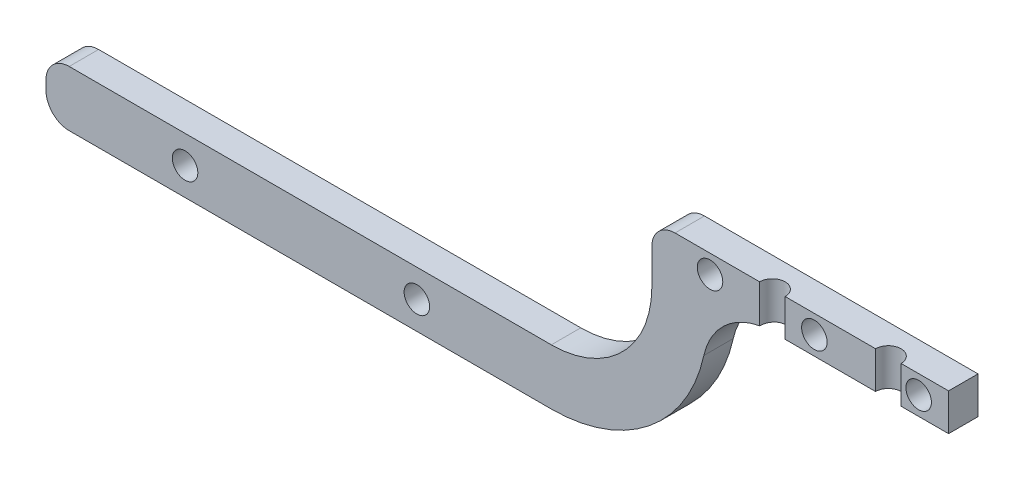
SolidWorks part; units mm, degrees
ref_plane "Front Plane" through (0, 0, 0) normal (0, 0, 1) x (1, 0, 0)
ref_plane "Top Plane" through (0, 0, 0) normal (0, 1, 0) x (1, 0, 0)
ref_plane "Right Plane" through (0, 0, 0) normal (1, 0, 0) x (0, 0, -1)
sketch "Sketch1" plane through (0, 0, 0) normal (0, 0, 1) x (1, 0, 0)
  line L0 (0, 0) -> (-64, 0)
  line L1 (-64, 0) -> (-64, -12.5522)
  line L2 (0, 0) -> (0, -8)
  line L3 (0, -8) -> (-52, -8)
  line L4 (-85.6878, -34.24) -> (-194.6878, -34.24)
  line L5 (-194.6878, -34.24) -> (-194.6878, -46.24)
  line L6 (-194.6878, -46.24) -> (-85.6878, -46.24)
  line L7 (-52, -12.5522) -> (-52, -8)
  arc A0 (-64, -12.5522) -> (-85.6878, -34.24) centre (-85.6878, -12.5522) cw
  arc A2 (-85.6878, -46.24) -> (-52, -12.5522) centre (-85.6878, -12.5522) ccw
  dimension "D4" = 4.5522
  dimension "D1" = 64
  dimension "D2" = 8
  dimension "D3" = 26.24
  dimension "D5" = 109
  dimension "D6" = 12
extrude "Boss-Extrude1" add sketch "Sketch1" along normal blind 6.35
fillet "Fillet1" radius 5 3 edges at (-64, 0, 3.175) (-194.6878, -46.24, 3.175) (-194.6878, -34.24, 3.175)
sketch "Sketch3" plane through (0, 0, 0) normal (0, 1, 0) x (1, 0, 0)
  line L0 (0, -3.175) -> (-59, -3.175) construction
  line L1 (0, -6.35) -> (0, 0) construction
  line L2 (-59, 0) -> (-59, -6.35) construction
  line L4 (0, -6.35) -> (-59, -6.35) construction
  circle A0 centre (-13, -6.35) radius 2.75
  circle A1 centre (-38, -6.35) radius 2.75
  point P8 (0, 0)
  point P11 (0, 0)
  point P12 (0, 0)
  point P13 (0, 0)
  point P14 (-38, -6.35)
  dimension "D1" = 5.5
  dimension "D2" = 5.5
  dimension "D3" = 25
  dimension "D4" = 13
fillet "Fillet2" radius 15 1 edges at (-52, -8, 3.175)
sketch "Sketch4" plane through (0, 0, 6.35) normal (0, 0, 1) x (1, 0, 0)
  line L0 (-181.7526, -34.24) -> (-181.7526, -46.24) construction
  line L1 (-85.6878, -34.24) -> (-189.6878, -34.24) construction
  line L2 (-189.6878, -46.24) -> (-85.6878, -46.24) construction
  line L3 (-181.7526, -40.24) -> (-194.6878, -40.24) construction
  line L4 (-194.6878, -39.24) -> (-194.6878, -41.24) construction
  line L5 (-66.4979, -40.24) -> (-181.7526, -40.24) construction
  line L6 (0, -4) -> (-63.899, -4) construction
  line L7 (0, -8) -> (0, 0) construction
  line L8 (-6.4525, 0) -> (-6.4525, -8) construction
  line L9 (0, 0) -> (-59, 0) construction
  line L10 (-38.1342, -8) -> (0, -8) construction
  line L11 (-28.9525, 0) -> (-28.9525, -8) construction
  line L12 (-51.4525, 0) -> (-51.4525, -16.0991) construction
  arc A0 (-85.6878, -46.24) -> (-52.7848, -19.7812) centre (-85.6878, -12.5522) ccw construction
  circle A1 centre (-164.6878, -40.24) radius 2.75
  circle A2 centre (-114.6878, -40.24) radius 2.75
  arc A3 (-59, 0) -> (-64, -5) centre (-59, -5) ccw construction
  arc A4 (-38.1342, -8) -> (-52.7848, -19.7812) centre (-38.1342, -23) ccw construction
  circle A5 centre (-6.4525, -4) radius 2.75
  circle A6 centre (-28.9525, -4) radius 2.75
  circle A7 centre (-51.4525, -4) radius 2.75
  dimension "D1" = 5.5
  dimension "D2" = 5.5
  dimension "D5" = 5.5
  dimension "D6" = 5.5
  dimension "D7" = 5.5
  dimension "D3" = 50
  dimension "D4" = 30
  dimension "D8" = 22.5
  dimension "D9" = 22.5
extrude "Cut-Extrude2" cut sketch "Sketch4" against normal blind 10
extrude "Cut-Extrude3" cut sketch "Sketch3" against normal up to next
